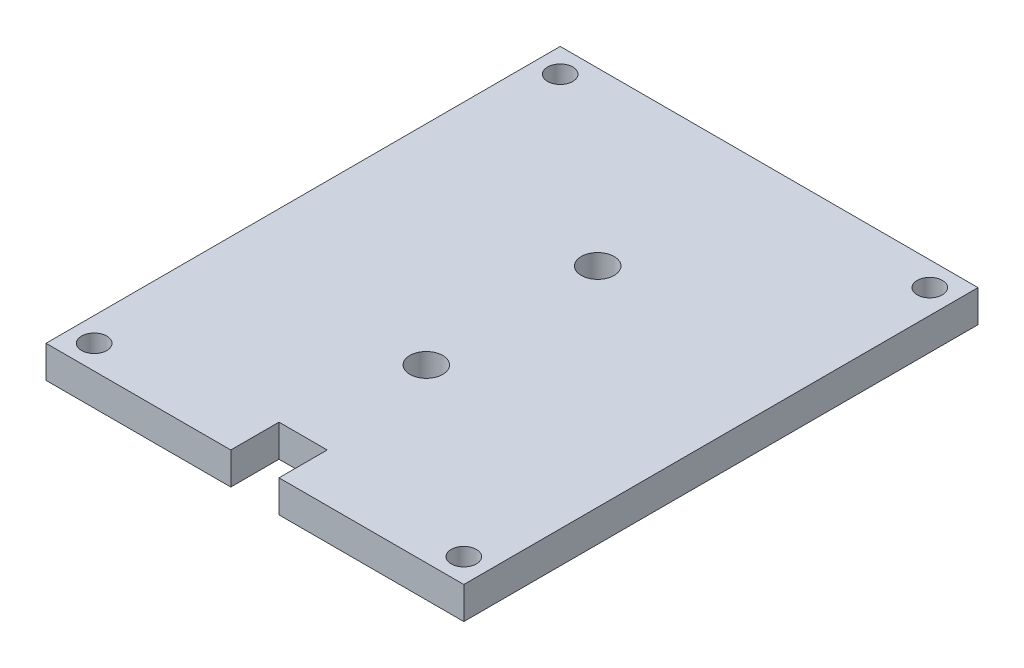
SolidWorks part; units mm, degrees
material "Acrylic (Medium-high impact)"
ref_plane "Front" through (0, 0, 0) normal (0, 0, 1) x (1, 0, 0)
ref_plane "Top" through (0, 0, 0) normal (0, 1, 0) x (1, 0, 0)
ref_plane "Right" through (0, 0, 0) normal (1, 0, 0) x (0, 0, -1)
sketch "Sketch1" plane through (0, 0, 0) normal (0, 1, 0) x (1, 0, 0)
  line L0 (0, 46.0375) -> (0, -46.0375) construction
  line L1 (-41.275, 46.0375) -> (41.275, 46.0375)
  line L2 (-41.275, 46.0375) -> (-41.275, -55.5625)
  line L3 (-41.275, -55.5625) -> (-4.7625, -55.5625)
  line L4 (41.275, 46.0375) -> (41.275, -55.5625)
  line L5 (4.7625, -55.5625) -> (41.275, -55.5625)
  line L6 (-36.5125, 41.275) -> (36.5125, 41.275) construction
  line L7 (-36.5125, 41.275) -> (-36.5125, -50.8) construction
  line L8 (-36.5125, -50.8) -> (36.5125, -50.8) construction
  line L9 (36.5125, 41.275) -> (36.5125, -50.8) construction
  line L11 (-4.7625, -55.5625) -> (-4.7625, -46.0375)
  line L12 (-4.7625, -46.0375) -> (4.7625, -46.0375)
  line L13 (4.7625, -55.5625) -> (4.7625, -46.0375)
  circle A0 centre (-36.5125, 41.275) radius 2.4892
  circle A1 centre (36.5125, 41.275) radius 2.4892
  circle A2 centre (36.5125, -50.8) radius 2.4892
  circle A3 centre (-36.5125, -50.8) radius 2.4892
  circle A4 centre (0, 12.1708) radius 3.2512
  circle A5 centre (0, -21.6958) radius 3.2512
  point P6 (0, 0)
  point P24 (0, -46.0375)
  point P25 (0, -42.9557)
  point P26 (0, -46.1772)
  dimension "D7" = 4.9784
  dimension "D8" = 6.5024
  dimension "D1" = 82.55
  dimension "D2" = 101.6
  dimension "D3" = 4.7625
  dimension "D4" = 4.7625
  dimension "D5" = 4.7625
  dimension "D6" = 4.7625
  dimension "D9" = 33.8667
  dimension "D10" = 33.8667
  dimension "D11" = 9.525
  dimension "D12" = 9.525
extrude "Boss-Extrude1" add sketch "Sketch1" along normal blind 6.35
